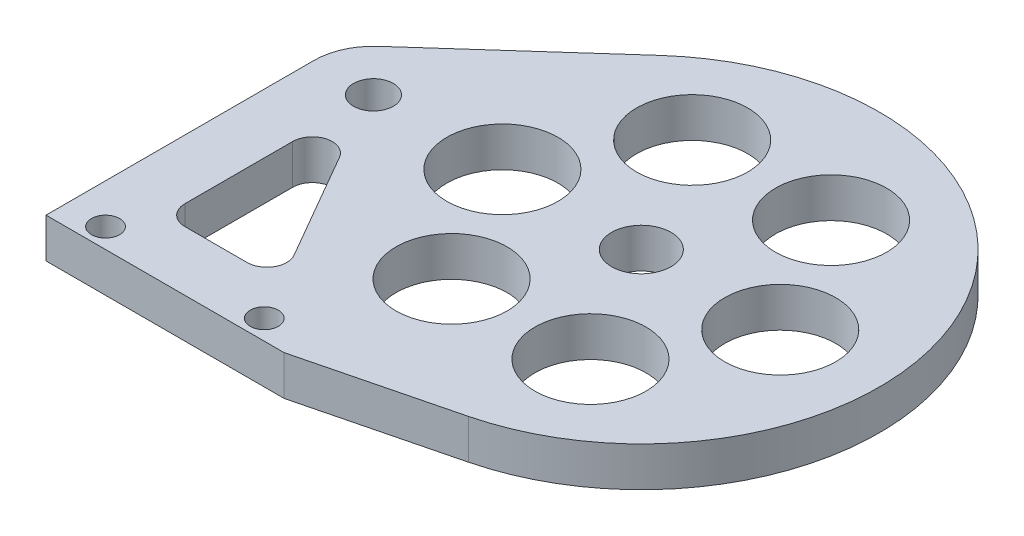
SolidWorks part; units mm, degrees
ref_plane "Front Plane" through (0, 0, 0) normal (0, 0, 1) x (1, 0, 0)
ref_plane "Top Plane" through (0, 0, 0) normal (0, 1, 0) x (1, 0, 0)
ref_plane "Right Plane" through (0, 0, 0) normal (1, 0, 0) x (0, 0, -1)
sketch "Sketch1" plane through (0, 0, 0) normal (0, 1, 0) x (1, 0, 0)
  line L0 (-52.3875, -42.8625) -> (-52.3875, 0)
  line L1 (-49.2125, 7.0995) -> (-25.4, 28.3981)
  line L3 (38.1, 0) -> (38.1, -42.8625)
  line L4 (38.1, -42.8625) -> (-52.3875, -42.8625)
  arc A0 (-49.2125, 7.0995) -> (-52.3875, 0) centre (-42.8625, 0) ccw
  arc A1 (-25.4, 28.3981) -> (38.1, 0) centre (0, 0) cw
  dimension "D1" = 9.525
  dimension "D2" = 38.1
  dimension "D3" = 42.8625
  dimension "D4" = 42.8625
extrude "Boss-Extrude1" add sketch "Sketch1" along normal blind 6.35
hole_wizard "1/4 (0.25) Diameter Hole1" positions "Sketch2" profile "Sketch3" hole size "1/4" standard "ANSI Inch"
sketch "Sketch2" plane through (0, 6.35, 0) normal (0, 1, 0) x (1, 0, 0)
  point P0 (-42.8625, 0)
sketch "Sketch3" plane through (-42.8625, 6.35, 0) normal (1, 0, 0) x (0, 0, 1)
  line L0 (0, 0) -> (0, 18.4177)
  line L1 (0, 18.4177) -> (3.175, 16.51)
  line L2 (3.175, 16.51) -> (3.175, 0)
  line L5 (3.175, 0) -> (0, 0)
  line L10 (0, 18.4177) -> (-3.175, 16.51) construction
  line L11 (0, -6.35) -> (0, 107.95) construction
  dimension "Hole Dia." = 6.35
  dimension "Hole Depth" = 16.51
  dimension "Drill Angle" = 118
hole_wizard "#8 Clearance Hole1" positions "Sketch4" profile "Sketch5" hole size "#8" standard "ANSI Inch"
sketch "Sketch4" plane through (0, 6.35, 0) normal (0, 1, 0) x (1, 0, 0)
  line L0 (-52.3875, -39.6875) -> (38.1, -39.6875)
  line L1 (-52.3875, 0) -> (-52.3875, -42.8625) construction
  line L2 (38.1, -42.8625) -> (38.1, 0) construction
  line L4 (-52.3875, -42.8625) -> (38.1, -42.8625) construction
  point P0 (-46.0375, -39.6875)
  point P20 (-20.6375, -39.6875)
  dimension "D1" = 3.175
  dimension "D2" = 25.4
  dimension "D3" = 6.35
sketch "Sketch5" plane through (-46.0375, 6.35, 39.6875) normal (1, 0, 0) x (0, 0, 1)
  line L0 (0, 0) -> (0, 17.8607)
  line L1 (0, 17.8607) -> (2.2479, 16.51)
  line L2 (2.2479, 16.51) -> (2.2479, 0)
  line L5 (2.2479, 0) -> (0, 0)
  line L10 (0, 17.8607) -> (-2.2479, 16.51) construction
  line L11 (0, -6.35) -> (0, 107.95) construction
  dimension "Hole Dia." = 4.4958
  dimension "Hole Depth" = 16.51
  dimension "Drill Angle" = 118
sketch "Sketch7" plane through (0, 6.35, 0) normal (0, 1, 0) x (1, 0, 0)
  circle A0 centre (0, 0) radius 4.7625
  dimension "D1" = 9.525
extrude "Cut-Extrude1" cut sketch "Sketch7" against normal through all
sketch "Sketch8" plane through (0, 6.35, 0) normal (0, 1, 0) x (1, 0, 0)
  line L0 (-14.2875, -42.8625) -> (9.2673, -36.9558)
  line L1 (-52.3875, -42.8625) -> (38.1, -42.8625) construction
  line L2 (38.1, -42.8625) -> (38.1, 0) construction
  line L3 (-14.2875, -42.8625) -> (38.1, -42.8625)
  line L4 (38.1, -42.8625) -> (38.1, 0)
  arc A0 (38.1, 0) -> (9.2673, -36.9558) centre (0, 0) cw
  circle A1 centre (-20.6375, -39.6875) radius 2.2479 construction
  dimension "D1" = 6.35
extrude "Cut-Extrude2" cut sketch "Sketch8" against normal through all
sketch "Sketch9" plane through (0, 6.35, 0) normal (0, 1, 0) x (1, 0, 0)
  line L0 (-42.8625, -12.9341) -> (-42.8625, -30.1625)
  line L1 (-39.6875, -33.3375) -> (-29.7407, -33.3375)
  line L2 (-26.991, -28.575) -> (-36.9379, -11.3466)
  line L3 (-52.3875, -42.8625) -> (-14.2875, -42.8625) construction
  line L4 (-52.3875, 0) -> (-52.3875, -42.8625) construction
  line L5 (-29.924, -4.445) -> (-18.8115, -23.6924) construction
  circle A0 centre (-22.225, 0) radius 8.89
  circle A1 centre (-11.1125, 19.2474) radius 8.89
  circle A2 centre (11.1125, 19.2474) radius 8.89
  circle A3 centre (22.225, 0) radius 8.89
  circle A4 centre (11.1125, -19.2474) radius 8.89
  circle A5 centre (-11.1125, -19.2474) radius 8.89
  arc A8 (-26.991, -28.575) -> (-29.7407, -33.3375) centre (-29.7407, -30.1625) cw
  arc A9 (-39.6875, -33.3375) -> (-42.8625, -30.1625) centre (-39.6875, -30.1625) cw
  arc A10 (-36.9379, -11.3466) -> (-42.8625, -12.9341) centre (-39.6875, -12.9341) ccw
  point P15 (0, 0)
  dimension "D1" = 17.78
  dimension "D4" = 9.525
  dimension "D7" = 3.175
  dimension "D2" = 22.225
  dimension "D5" = 9.525
  dimension "D6" = 9.525
  dimension "D3" = 6
extrude "Cut-Extrude3" cut sketch "Sketch9" against normal through all
